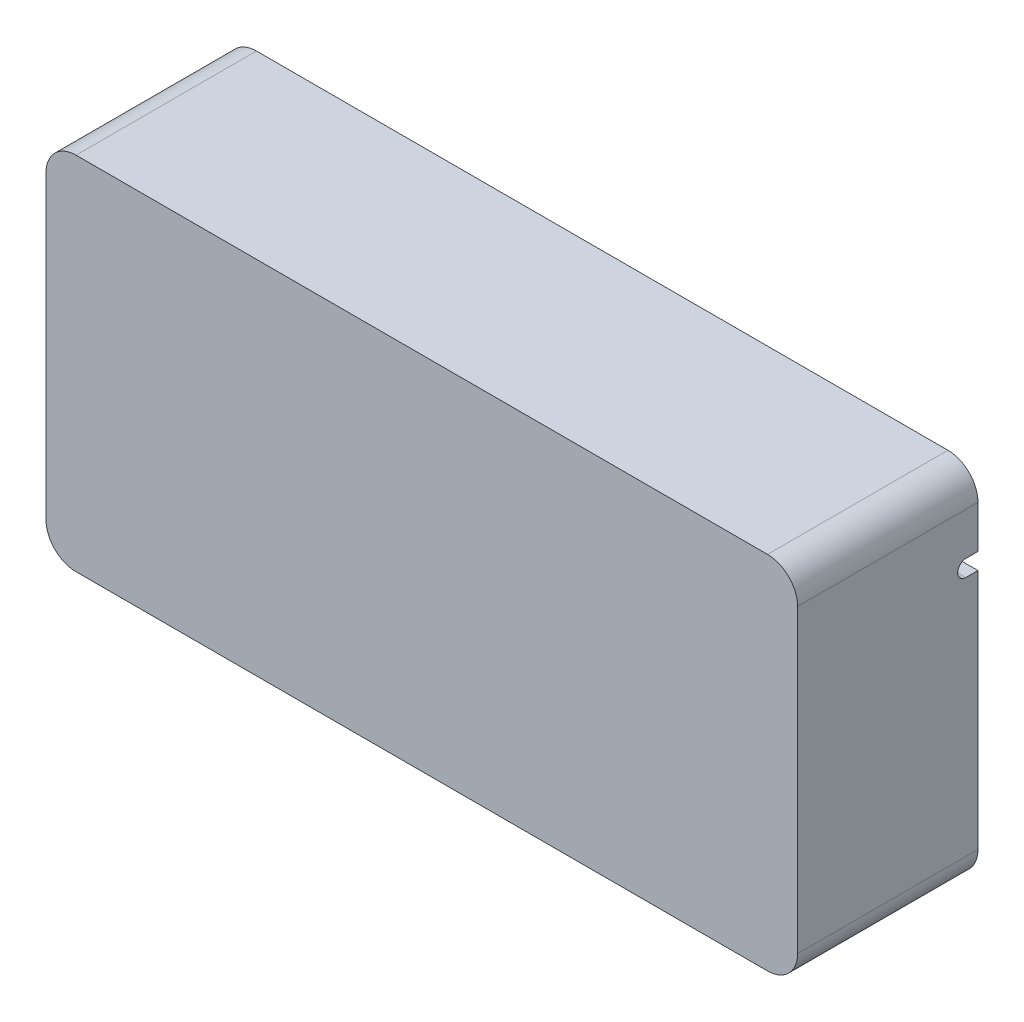
SolidWorks part; units mm, degrees
material "ABS"
ref_plane "Front Plane" through (0, 0, 0) normal (0, 0, 1) x (1, 0, 0)
ref_plane "Top Plane" through (0, 0, 0) normal (0, 1, 0) x (1, 0, 0)
ref_plane "Right Plane" through (0, 0, 0) normal (1, 0, 0) x (0, 0, -1)
sketch "Sketch1" plane through (0, 0, 0) normal (0, 0, 1) x (1, 0, 0)
  line L1 (-158.75, 76.2) -> (158.75, 76.2)
  line L2 (-158.75, 76.2) -> (-158.75, -76.2)
  line L3 (-158.75, -76.2) -> (158.75, -76.2)
  line L4 (158.75, 76.2) -> (158.75, -76.2)
  point P4 (0, 76.2)
  point P6 (-158.75, 0)
  dimension "D1" = 317.5
  dimension "D2" = 152.4
extrude "Boss-Extrude1" add sketch "Sketch1" along normal blind 76.2
sketch "Sketch2" plane through (0, 0, 0) normal (0, 0, -1) x (-1, 0, 0)
  line L8 (151.13, -68.58) -> (151.13, 68.58)
  line L9 (151.13, 68.58) -> (-151.13, 68.58)
  line L10 (-151.13, 68.58) -> (-151.13, -68.58)
  line L11 (-151.13, -68.58) -> (151.13, -68.58)
  line L12 (151.13, -68.58) -> (151.13, 68.58)
  line L13 (151.13, 68.58) -> (-151.13, 68.58)
  line L14 (-151.13, 68.58) -> (-151.13, -68.58)
  line L15 (-151.13, -68.58) -> (151.13, -68.58)
  dimension "D1" = 7.62
extrude "Cut-Extrude1" cut sketch "Sketch2" against normal offset from surface (68.58 mm away) 7.62 up to face at (0, 0, 76.2)
sketch "Sketch3" plane through (-158.75, 0, 0) normal (-1, 0, 0) x (0, 0, 1)
  line L0 (42.037, 38.5445) -> (0, 38.5445)
  line L1 (0, 76.2) -> (0, -76.2) construction
  line L2 (42.037, 45.5295) -> (0, 45.5295)
  line L3 (0, 45.5295) -> (0, 38.5445)
  arc A1 (42.037, 38.5445) -> (42.037, 45.5295) centre (42.037, 42.037) ccw
  dimension "D1" = 6.985
extrude "Cut-Extrude2" cut sketch "Sketch3" against normal up to next
sketch "Sketch4" plane through (0, 0, 68.58) normal (0, 0, -1) x (-1, 0, 0)
  line L0 (-151.13, 0) -> (0, 0)
  line L1 (-151.13, 68.58) -> (-151.13, -68.58) construction
  line L2 (0, 0) -> (0, -68.58)
  line L3 (-151.13, -68.58) -> (151.13, -68.58) construction
  line L4 (0, -68.58) -> (-7.112, -68.58)
  line L5 (-7.112, -68.58) -> (-7.112, -6.35)
  line L6 (-7.112, -6.35) -> (-151.13, -6.35)
  line L7 (-151.13, -6.35) -> (-151.13, 0)
  line L8 (-9.652, -63.5) -> (-9.652, -11.43) construction
  line L9 (-148.59, -8.89) -> (-12.192, -8.89) construction
  dimension "D1" = 2.54
  dimension "D2" = 2.54
extrude "Boss-Extrude2" add sketch "Sketch4" along normal blind 25.4
sketch "Sketch5" plane through (151.13, 0, 0) normal (-1, 0, 0) x (0, 0, 1)
  line L0 (42.037, 42.037) -> (0, 42.037) construction
  line L1 (0, 68.58) -> (0, -68.58) construction
  line L2 (5.08, 38.5445) -> (0, 38.5445)
  line L3 (5.08, 45.5295) -> (0, 45.5295)
  line L4 (0, 45.5295) -> (0, 38.5445)
  arc A0 (5.08, 38.5445) -> (5.08, 45.5295) centre (5.08, 42.037) ccw
  dimension "D1" = 5.08
extrude "Cut-Extrude3" cut sketch "Sketch5" against normal up to next
sketch "Sketch7" plane through (0, 0, 68.58) normal (0, 0, -1) x (-1, 0, 0)
  circle A1 centre (140.01, -63.81) radius 3
  circle A3 centre (82.01, -63.81) radius 3
  circle A5 centre (140.01, -14.81) radius 3
  circle A7 centre (82.01, -14.81) radius 3
extrude "Boss-Extrude4" add sketch "Sketch7" along normal blind 7.62
fillet "Fillet2" radius 12.7 8 edges at (-151.13, -68.58, 34.29) (-158.75, -76.2, 38.1) (-151.13, 68.58, 34.29) (-158.75, 76.2, 38.1) (158.75, 76.2, 38.1) (151.13, 68.58, 34.29) (151.13, -68.58, 34.29) (158.75, -76.2, 38.1)
fillet "Fillet3" radius 2.54 8 edges at (7.112, -68.58, 55.88) (3.556, -68.58, 43.18) (0, -68.58, 55.88) (0, 0, 55.88) (7.112, -6.35, 55.88) (151.13, 0, 55.88) (151.13, -3.175, 43.18) (151.13, -6.35, 55.88)
